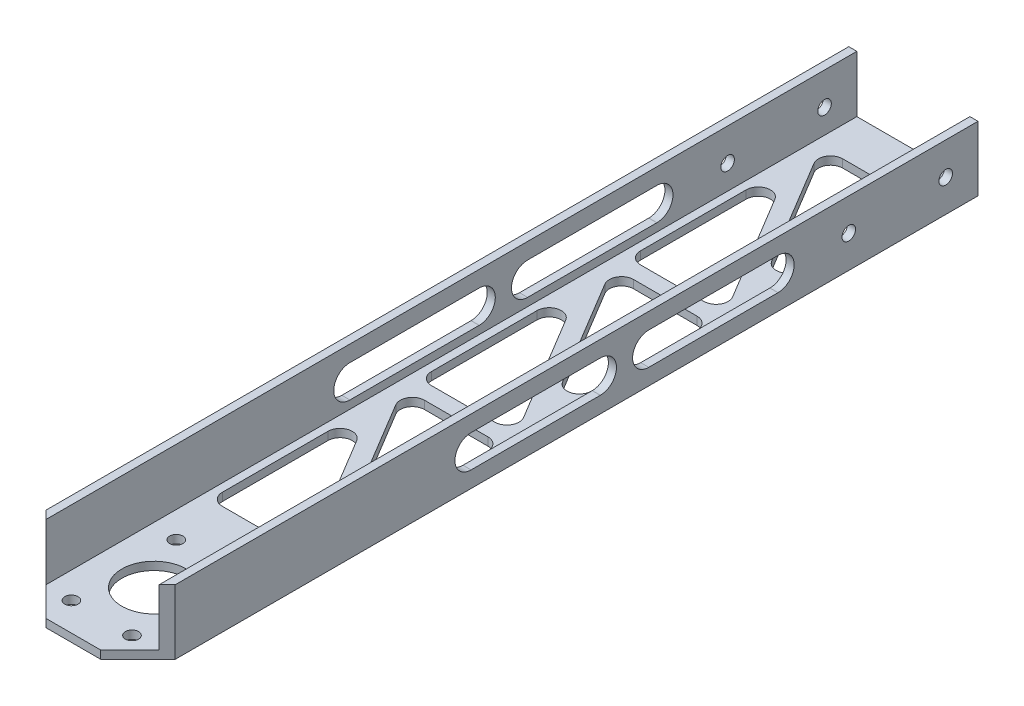
SolidWorks part; units mm, degrees
material "6063-T6"
ref_plane "Front" through (0, 0, 0) normal (0, 0, 1) x (1, 0, 0)
ref_plane "Top" through (0, 0, 0) normal (0, 1, 0) x (1, 0, 0)
ref_plane "Right" through (0, 0, 0) normal (1, 0, 0) x (0, 0, -1)
sketch "Sketch1" plane through (0, 0, 0) normal (0, 0, 1) x (1, 0, 0)
  line L0 (47.625, 3.175) -> (47.625, 25.4)
  line L1 (0, 0) -> (50.8, 0)
  line L2 (0, 0) -> (0, 25.4)
  line L4 (50.8, 0) -> (50.8, 25.4)
  line L5 (3.175, 3.175) -> (47.625, 3.175)
  line L6 (3.175, 3.175) -> (3.175, 25.4)
  line L7 (50.8, 25.4) -> (47.625, 25.4)
  line L8 (0, 25.4) -> (3.175, 25.4)
  dimension "D1" = 25.4
  dimension "D2" = 50.8
  dimension "D3" = 3.175
extrude "Boss-Extrude1" add sketch "Sketch1" along normal blind 330.2
sketch "Sketch2" plane through (0, 0, 0) normal (0, -1, 0) x (1, 0, 0)
  line L0 (25.4, 298.45) -> (25.4, 330.2) construction
  line L1 (0, 330.2) -> (50.8, 330.2) construction
  circle A0 centre (25.4, 298.45) radius 12.7
  dimension "D1" = 25.4
  dimension "D2" = 31.75
extrude "Cut-Extrude1" cut sketch "Sketch2" against normal up to next
sketch "Sketch3" plane through (50.8, 0, 0) normal (1, 0, 0) x (0, 0, -1)
  line L0 (-12.7, 12.7) -> (0, 12.7) construction
  line L1 (0, 0) -> (0, 25.4) construction
  line L2 (-12.7, 12.7) -> (-50.8, 12.7) construction
  circle A0 centre (-12.7, 12.7) radius 2.667
  circle A1 centre (-50.8, 12.7) radius 2.667
  dimension "D1" = 5.334
  dimension "D4" = 5.334
  dimension "D2" = 12.7
  dimension "D3" = 38.1
extrude "Cut-Extrude2" cut sketch "Sketch3" against normal through all
sketch "Sketch4" plane through (0, 0, 0) normal (0, -1, 0) x (1, 0, 0)
  circle A1 centre (13.4937, 277.8278) radius 2.5908
  circle A3 centre (37.3062, 277.8278) radius 2.5908
  circle A5 centre (13.4937, 319.0722) radius 2.5908
  circle A7 centre (37.3062, 319.0722) radius 2.5908
extrude "Cut-Extrude3" cut sketch "Sketch4" against normal up to next
sketch "Sketch5" plane through (0, 0, 0) normal (0, -1, 0) x (1, 0, 0)
  line L8 (0, 330.2) -> (0, 0) construction
  line B0 (40.1223, 85.7734) -> (15.1963, 44.23)
  line B1 (6.35, 40.4053) -> (0, 40.4053) construction
  line B2 (14.7615, 17.144) -> (39.6875, 17.144)
  line B3 (6.35, 17.144) -> (6.35, 80.644) construction
  line B4 (6.35, 80.644) -> (44.45, 80.644) construction
  line B5 (44.45, 21.9065) -> (44.45, 63.4499)
  line B6 (10.6777, 24.3568) -> (35.6037, 65.9001)
  line B7 (6.35, 80.644) -> (44.45, 17.144) construction
  line B8 (44.45, 37.6448) -> (50.8, 37.6448) construction
  arc B9 (35.6037, 65.9001) -> (44.45, 63.4499) centre (39.6875, 63.4499) cw
  arc B10 (39.6875, 17.144) -> (44.45, 21.9065) centre (39.6875, 21.9065) ccw
  arc B11 (10.6777, 24.3568) -> (14.7615, 17.144) centre (14.7615, 21.9065) ccw
  line B12 (36.0385, 92.9862) -> (11.1125, 92.9862)
  arc B13 (40.1223, 85.7734) -> (36.0385, 92.9862) centre (36.0385, 88.2237) ccw
  arc B14 (11.1125, 92.9862) -> (6.35, 88.2237) centre (11.1125, 88.2237) ccw
  line B15 (6.35, 88.2237) -> (6.35, 46.6803)
  arc B16 (15.1963, 44.23) -> (6.35, 46.6803) centre (11.1125, 46.6803) cw
  line B17 (40.1223, 167.9656) -> (15.1963, 126.4222)
  line B18 (14.7615, 99.3362) -> (39.6875, 99.3362)
  line B19 (44.45, 104.0987) -> (44.45, 145.642)
  line B20 (10.6777, 106.549) -> (35.6037, 148.0923)
  arc B21 (35.6037, 148.0923) -> (44.45, 145.642) centre (39.6875, 145.642) cw
  arc B22 (39.6875, 99.3362) -> (44.45, 104.0987) centre (39.6875, 104.0987) ccw
  arc B23 (10.6777, 106.549) -> (14.7615, 99.3362) centre (14.7615, 104.0987) ccw
  line B24 (36.0385, 175.1784) -> (11.1125, 175.1784)
  arc B25 (40.1223, 167.9656) -> (36.0385, 175.1784) centre (36.0385, 170.4159) ccw
  arc B26 (11.1125, 175.1784) -> (6.35, 170.4159) centre (11.1125, 170.4159) ccw
  line B27 (6.35, 170.4159) -> (6.35, 128.8725)
  arc B28 (15.1963, 126.4222) -> (6.35, 128.8725) centre (11.1125, 128.8725) cw
  line B29 (40.1223, 250.1577) -> (15.1963, 208.6144)
  line B30 (14.7615, 181.5284) -> (39.6875, 181.5284)
  line B31 (44.45, 186.2909) -> (44.45, 227.8342)
  line B32 (10.6777, 188.7411) -> (35.6037, 230.2845)
  arc B33 (35.6037, 230.2845) -> (44.45, 227.8342) centre (39.6875, 227.8342) cw
  arc B34 (39.6875, 181.5284) -> (44.45, 186.2909) centre (39.6875, 186.2909) ccw
  arc B35 (10.6777, 188.7411) -> (14.7615, 181.5284) centre (14.7615, 186.2909) ccw
  line B36 (36.0385, 257.3705) -> (11.1125, 257.3705)
  arc B37 (40.1223, 250.1577) -> (36.0385, 257.3705) centre (36.0385, 252.608) ccw
  arc B38 (11.1125, 257.3705) -> (6.35, 252.608) centre (11.1125, 252.608) ccw
  line B39 (6.35, 252.608) -> (6.35, 211.0647)
  arc B40 (15.1963, 208.6144) -> (6.35, 211.0647) centre (11.1125, 211.0647) cw
  dimension "D1" = 6.35
  dimension "D2" = 6.35
sketch_block_instance "Block2-1"
sketch_block "Block2" parameters "D1"=6.35
sketch_block_instance "Block1-4"
sketch_block "Block1" parameters "D3"=4.7625, "D1"=63.5, "D2"=38.1
sketch_block_instance "Block1-1"
sketch_block_instance "Block2-2"
sketch_block_instance "Block2-4"
extrude "Cut-Extrude4" cut sketch "Sketch5" against normal up to next
sketch "Sketch6" plane through (0, 0, 0) normal (-1, 0, 0) x (0, 0, 1)
  line L0 (78.617, 12.7) -> (129.417, 12.7) construction
  line L1 (78.617, 19.05) -> (129.417, 19.05)
  line L2 (78.617, 6.35) -> (129.417, 6.35)
  line L3 (330.2, 25.4) -> (0, 25.4) construction
  line L4 (84.874, 19.05) -> (84.874, 25.4) construction
  line L5 (88.704, 6.35) -> (88.704, 0) construction
  line L6 (330.2, 0) -> (0, 0) construction
  line L7 (154.724, 19.05) -> (154.724, 25.4) construction
  line L8 (158.554, 6.35) -> (158.554, 0) construction
  line L9 (148.467, 12.7) -> (199.267, 12.7) construction
  line L10 (148.467, 19.05) -> (199.267, 19.05)
  line L11 (148.467, 6.35) -> (199.267, 6.35)
  arc A0 (78.617, 19.05) -> (78.617, 6.35) centre (78.617, 12.7) ccw
  arc A1 (129.417, 6.35) -> (129.417, 19.05) centre (129.417, 12.7) ccw
  arc A2 (148.467, 19.05) -> (148.467, 6.35) centre (148.467, 12.7) ccw
  arc A3 (199.267, 6.35) -> (199.267, 19.05) centre (199.267, 12.7) ccw
  point P2 (104.017, 12.7)
  point P18 (173.867, 12.7)
  dimension "D1" = 12.7
  dimension "D2" = 50.8
  dimension "D3" = 2
extrude "Cut-Extrude5" cut sketch "Sketch6" against normal through all
sketch "Sketch7" plane through (0, 0, 0) normal (0, -1, 0) x (1, 0, 0)
  line L5 (0, 330.2) -> (0, 315.5584)
  line L6 (0, 330.2) -> (0, 0) construction
  line L7 (0, 315.5584) -> (14.6416, 330.2)
  line L8 (0, 330.2) -> (50.8, 330.2) construction
  line L9 (14.6416, 330.2) -> (0, 330.2)
  line L10 (25.4, 330.2) -> (25.4, 320.5788) construction
  line L11 (36.1584, 330.2) -> (50.8, 330.2)
  line L12 (50.8, 315.5584) -> (36.1584, 330.2)
  line L13 (50.8, 330.2) -> (50.8, 315.5584)
extrude "Cut-Extrude6" cut sketch "Sketch7" against normal through all
